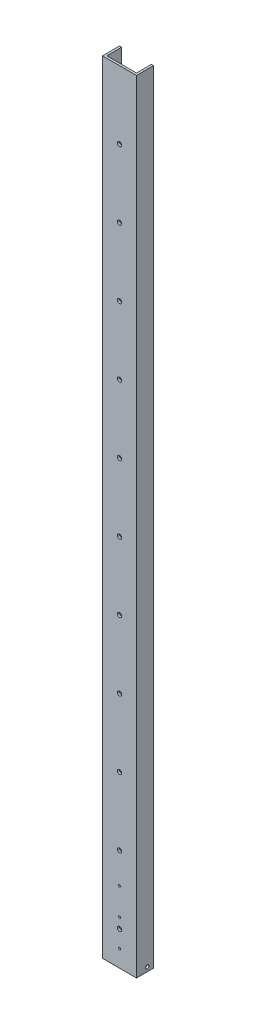
SolidWorks part; units mm, degrees
ref_plane "Front" through (0, 0, 0) normal (0, 0, 1) x (1, 0, 0)
ref_plane "Top" through (0, 0, 0) normal (0, 1, 0) x (1, 0, 0)
ref_plane "Right" through (0, 0, 0) normal (1, 0, 0) x (0, 0, -1)
sketch "Sketch1" plane through (0, 0, 0) normal (0, 1, 0) x (1, 0, 0)
  line L0 (3.175, 3.175) -> (3.175, 25.4)
  line L1 (0, 0) -> (50.8, 0)
  line L2 (0, 0) -> (0, 25.4)
  line L4 (50.8, 0) -> (50.8, 25.4)
  line L5 (3.175, 3.175) -> (47.625, 3.175)
  line L6 (47.625, 3.175) -> (47.625, 25.4)
  line L7 (0, 25.4) -> (3.175, 25.4)
  line L8 (50.8, 25.4) -> (47.625, 25.4)
  dimension "D1" = 25.4
  dimension "D2" = 50.8
  dimension "D3" = 3.175
extrude "Boss-Extrude1" add sketch "Sketch1" along normal blind 1168.4
sketch "Sketch2" plane through (0, 0, 0) normal (0, 0, 1) x (1, 0, 0)
  line L0 (25.4, 0) -> (25.4, 50.8) construction
  line L1 (0, 0) -> (50.8, 0) construction
  circle A0 centre (25.4, 50.8) radius 3.175
  circle A1 centre (25.4, 152.4) radius 3.175
  circle A2 centre (25.4, 254) radius 3.175
  circle A3 centre (25.4, 355.6) radius 3.175
  circle A4 centre (25.4, 457.2) radius 3.175
  circle A5 centre (25.4, 558.8) radius 3.175
  circle A6 centre (25.4, 660.4) radius 3.175
  circle A7 centre (25.4, 762) radius 3.175
  circle A8 centre (25.4, 863.6) radius 3.175
  circle A9 centre (25.4, 965.2) radius 3.175
  circle A10 centre (25.4, 1066.8) radius 3.175
  dimension "D2" = 6.35
  dimension "D1" = 50.8
  dimension "D3" = 11
extrude "Cut-Extrude1" cut sketch "Sketch2" against normal up to next
sketch "Sketch3" plane through (0, 0, -3.175) normal (0, 0, -1) x (-1, 0, 0)
  line L0 (-25.4, 0) -> (-25.4, 25.4) construction
  line L1 (-47.625, 0) -> (-3.175, 0) construction
  circle A0 centre (-25.4, 25.4) radius 1.5875
  circle A3 centre (-25.4, 66.0203) radius 1.5875 construction
  circle A4 centre (-25.4, 66.0203) radius 1.5875
  circle A5 centre (-25.4, 106.6406) radius 1.5875 construction
  circle A6 centre (-25.4, 106.6406) radius 1.5875
  dimension "D2" = 3.175
  dimension "D1" = 25.4
extrude "Cut-Extrude2" cut sketch "Sketch3" against normal up to next
sketch "Sketch4" plane through (0, 0, 0) normal (-1, 0, 0) x (0, 0, 1)
  line L0 (-15.875, 0) -> (-15.875, 6.35) construction
  line L2 (-25.4, 0) -> (0, 0) construction
  line L3 (-15.875, 6.35) -> (-25.4, 6.35) construction
  line L4 (-25.4, 1168.4) -> (-25.4, 0) construction
  circle A0 centre (-15.875, 6.35) radius 2.667
  dimension "D2" = 5.334
  dimension "D1" = 6.35
  dimension "D3" = 9.525
extrude "Cut-Extrude3" cut sketch "Sketch4" against normal through all
